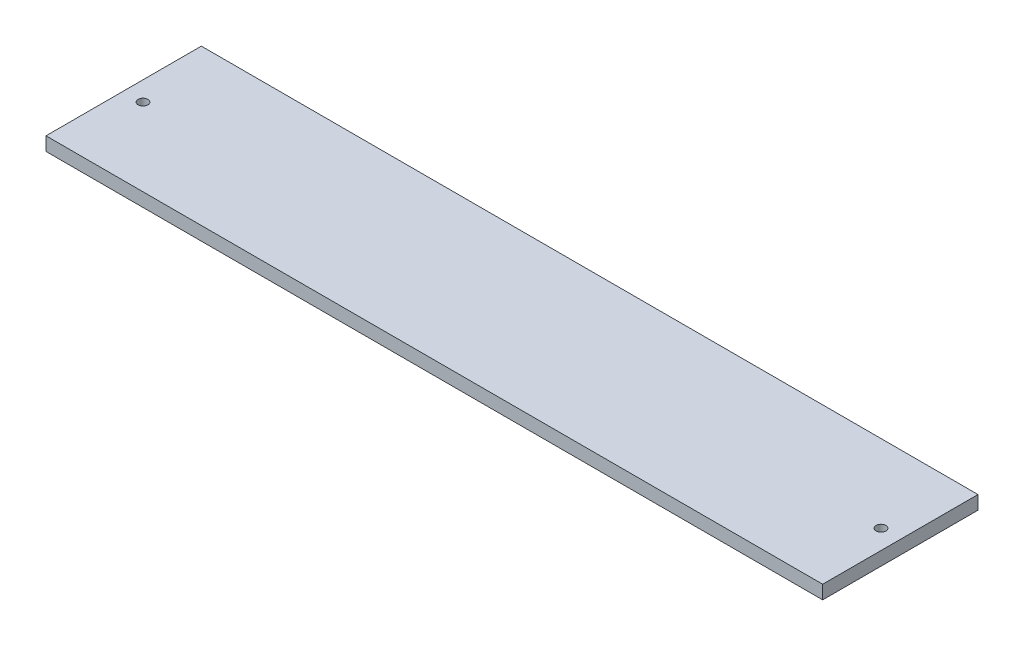
SolidWorks part; units mm, degrees
material "Pino"
ref_plane "Piano frontale" through (0, 0, 0) normal (0, 0, 1) x (1, 0, 0)
ref_plane "Piano superiore" through (0, 0, 0) normal (0, 1, 0) x (1, 0, 0)
ref_plane "Piano destro" through (0, 0, 0) normal (1, 0, 0) x (0, 0, -1)
sketch "Schizzo1" plane through (0, 0, 0) normal (0, 1, 0) x (1, 0, 0)
  line L1 (0, 0) -> (400, 0)
  line L2 (0, 0) -> (0, 80)
  line L3 (0, 80) -> (400, 80)
  line L4 (400, 0) -> (400, 80)
  dimension "D1" = 400
  dimension "D2" = 80
extrude "Estrusione-Estrusione1" add sketch "Schizzo1" along normal blind 7
extrude "Taglio-Estrusione1" cut sketch "Schizzo2" along direction (0, -1, 0) on the side against the normal blind 10
sketch "Schizzo2" plane through (109.6735, 0, 372.3761) normal (0, -1, 0) x (0, 0, 1)
  line L2 (-415.3761, 99.7184) -> (-409.3761, 99.7184) construction
  line L5 (-452.3761, -90.3265) -> (-372.3761, -90.3265) construction
  circle A2 centre (-412.3761, 99.7184) radius 2.5
  circle A3 centre (-412.3761, -280.3714) radius 2.5
